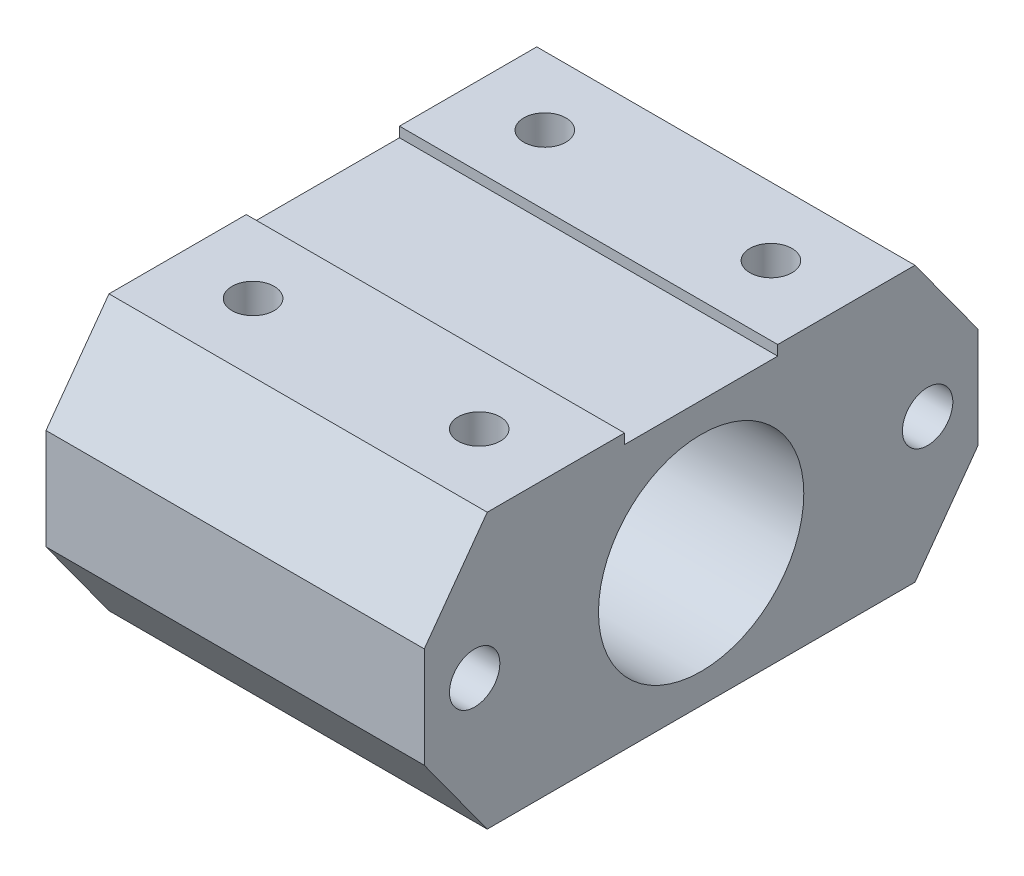
SolidWorks part; units mm, degrees
ref_plane "Front Plane" through (0, 0, 0) normal (0, 0, 1) x (1, 0, 0)
ref_plane "Top Plane" through (0, 0, 0) normal (0, 1, 0) x (1, 0, 0)
ref_plane "Right Plane" through (0, 0, 0) normal (1, 0, 0) x (0, 0, -1)
sketch "Sketch1" plane through (0, 0, 0) normal (0, 1, 0) x (1, 0, 0)
  line L0 (15.015, 33.96) -> (15.015, 0) construction
  line L1 (0, 0) -> (30.03, 0)
  line L2 (0, 0) -> (0, 33.96)
  line L3 (0, 33.96) -> (30.03, 33.96)
  line L4 (30.03, 0) -> (30.03, 33.96)
  line L5 (0, 28.56) -> (30.03, 28.56) construction
  line L6 (23.99, 33.96) -> (23.99, 0) construction
  line L7 (0, 16.98) -> (30.03, 16.98) construction
  circle A0 centre (23.99, 28.56) radius 1.675
  circle A1 centre (6.04, 28.56) radius 1.675
  circle A2 centre (23.99, 5.4) radius 1.675
  circle A3 centre (6.04, 5.4) radius 1.675
  dimension "D5" = 3.35
  dimension "D1" = 33.96
  dimension "D2" = 30.03
  dimension "D3" = 6.04
  dimension "D4" = 5.4
extrude "Boss-Extrude4" add sketch "Sketch1" along normal blind 21.79
sketch "Sketch5" plane through (30.03, 0, 0) normal (1, 0, 0) x (0, 0, -1)
  line L0 (33.96, 10.5) -> (0, 10.5) construction
  line L1 (33.96, 21.79) -> (33.96, 0) construction
  line L2 (0, 21.79) -> (0, 0) construction
  line L3 (0, 0) -> (33.96, 0) construction
  circle A0 centre (16.98, 10.5) radius 8.15
  dimension "D2" = 16.3
  dimension "D1" = 10.5
extrude "Cut-Extrude1" cut sketch "Sketch5" against normal through all
sketch "Sketch7" plane through (0, 21.79, 0) normal (0, 1, 0) x (1, 0, 0)
  line L0 (0, 33.96) -> (0, 0) construction
  line L1 (0, 23.06) -> (30.03, 23.06)
  line L2 (0, 23.06) -> (0, 10.9)
  line L3 (0, 10.9) -> (30.03, 10.9)
  line L4 (30.03, 23.06) -> (30.03, 10.9)
  line L5 (30.03, 33.96) -> (0, 33.96) construction
  line L6 (0, 0) -> (30.03, 0) construction
  line L7 (30.03, 0) -> (30.03, 33.96) construction
  dimension "D1" = 10.9
  dimension "D2" = 10.9
extrude "Cut-Extrude2" cut sketch "Sketch7" against normal blind 0.8
sketch "Sketch10" plane through (0, 0, 0) normal (-1, 0, 0) x (0, 0, 1)
  circle A0 centre (-16.98, 10.5) radius 8.15
  circle A1 centre (-16.98, 10.5) radius 8.15 construction
  circle A2 centre (-16.98, 10.5) radius 4.75
  dimension "D1" = 9.5
extrude "Boss-Extrude6" add sketch "Sketch10" against normal blind 3
sketch "Sketch12" plane through (0, 0, 0) normal (-1, 0, 0) x (0, 0, 1)
  line L0 (0, 10.895) -> (-33.96, 10.895) construction
  line L1 (0, 21.79) -> (0, 0) construction
  line L2 (-33.96, 21.79) -> (-33.96, 0) construction
  line L3 (5, 14.895) -> (0, 21.79)
  line L5 (-33.96, 14.895) -> (-33.96, 6.895)
  line L7 (-38.96, 14.895) -> (-38.96, 6.895)
  line L9 (0, 14.895) -> (0, 6.895)
  line L11 (5, 14.895) -> (5, 6.895)
  line L12 (0, 21.79) -> (0, 14.895)
  line L13 (5, 6.895) -> (0, 0)
  line L14 (0, 0) -> (0, 6.895)
  line L15 (-33.96, 14.895) -> (-33.96, 21.79)
  line L16 (-33.96, 21.79) -> (-38.96, 14.895)
  line L17 (-33.96, 6.895) -> (-33.96, 0)
  line L18 (-33.96, 0) -> (-38.96, 6.895)
  point P14 (0, 10.895)
  point P15 (-33.96, 10.895)
  point P16 (4.9334, 3.7331)
  point P25 (0, 0)
  point P26 (0, 0)
  point P27 (0, 0)
  dimension "D1" = 5
  dimension "D2" = 8
  dimension "D3" = 5
extrude "Boss-Extrude7" add sketch "Sketch12" against normal up to surface (30.03 mm away) up to face at (30.03, 16.1425, -16.98)
sketch "Sketch13" plane through (30.03, 0, 0) normal (1, 0, 0) x (0, 0, -1)
  line L0 (16.98, 20.99) -> (16.98, 0) construction
  line L1 (10.9, 20.99) -> (23.06, 20.99) construction
  line L2 (-5, 14.895) -> (-5, 6.895) construction
  line L3 (0, 0) -> (33.96, 0) construction
  line L4 (-5, 10.895) -> (38.96, 10.895) construction
  line L5 (38.96, 6.895) -> (38.96, 14.895) construction
  circle A0 centre (-1, 10.895) radius 2
  circle A1 centre (34.96, 10.895) radius 2
  point P18 (-1, 10.895)
  dimension "D2" = 4
  dimension "D1" = 4
extrude "Cut-Extrude4" cut sketch "Sketch13" against normal blind 10
equation "\"8mm hole\" = 8.6mm"
equation "\"22mm hole\"= 23mm"
equation "\"15mm hole\"= 15.8mm"
equation "\"bed height offset\"= 3mm"
equation "\"D2@Sketch5\"=\"15mm hole\" + 0.5"
